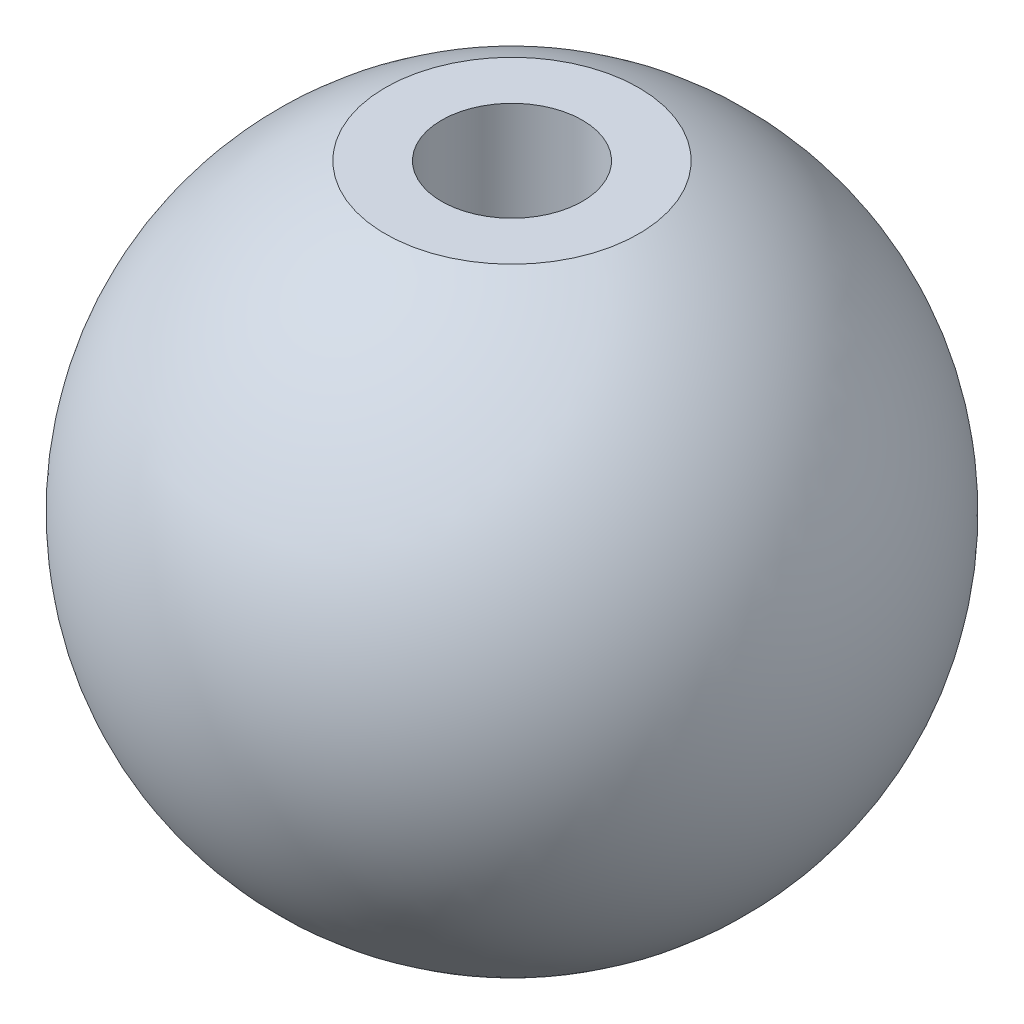
SolidWorks part; units mm, degrees
ref_plane "Front Plane" through (0, 0, 0) normal (0, 0, 1) x (1, 0, 0)
ref_plane "Top Plane" through (0, 0, 0) normal (0, 1, 0) x (1, 0, 0)
ref_plane "Right Plane" through (0, 0, 0) normal (1, 0, 0) x (0, 0, -1)
sketch "Sketch1" plane through (0, 0, 0) normal (0, 0, 1) x (1, 0, 0)
  line L0 (0, 11.1051) -> (0, -12.2949)
  arc A0 (0, -12.2949) -> (0, 11.1051) centre (0, -0.5949) cw
  dimension "D1" = 23.4
revolve "Revolve1" add sketch "Sketch1" angle 360 about L0
sketch "Sketch2" plane through (0, 0, 0) normal (0, 1, 0) x (1, 0, 0)
  circle A0 centre (0, 0) radius 2.5
  dimension "D1" = 5
extrude "Cut-Extrude1" cut sketch "Sketch2" against normal through all both and the other way through all
sketch "Sketch6" plane through (0, 0, 0) normal (0, 0, 1) x (1, 0, 0)
  line L0 (0, 10.8349) -> (0, -12.0247) construction
  line L1 (-2.5, 10.8349) -> (2.5, 10.8349) construction
  line L2 (-2.5, -12.0247) -> (2.5, -12.0247) construction
  line L3 (0, -0.5949) -> (0, -13.3949) construction
  line L4 (0, -0.5949) -> (0, 12.2051) construction
  line L5 (0, 12.2051) -> (-13.7686, 12.2051)
  line L6 (-13.7686, 12.2051) -> (-13.7686, 10.2051)
  line L7 (-13.7686, 10.2051) -> (12.6313, 10.2051)
  line L8 (12.6313, 10.2051) -> (12.6313, 12.2051)
  line L9 (12.6313, 12.2051) -> (0, 12.2051)
  line L10 (0, -13.3949) -> (12.6313, -13.3949)
  line L11 (12.6313, -13.3949) -> (12.6313, -11.3949)
  line L12 (12.6313, -11.3949) -> (-13.7686, -11.3949)
  line L13 (-13.7686, -11.3949) -> (-13.7686, -13.3949)
  line L14 (-13.7686, -13.3949) -> (0, -13.3949)
  dimension "D1" = 22.8596
  dimension "D2" = 12.8
  dimension "D3" = 12.8
  dimension "D4" = 2
  dimension "D5" = 2
extrude "Cut-Extrude2" cut sketch "Sketch6" against normal through all both and the other way through all
